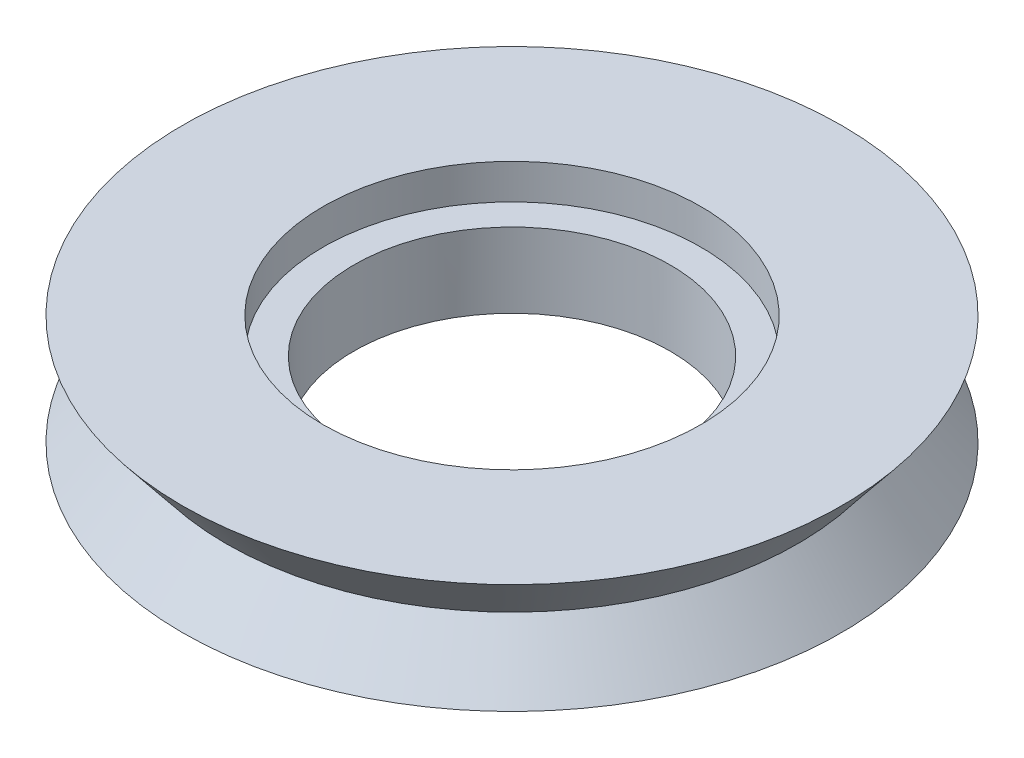
SolidWorks part; units mm, degrees
ref_plane "정면" through (0, 0, 0) normal (0, 0, 1) x (1, 0, 0)
ref_plane "윗면" through (0, 0, 0) normal (0, 1, 0) x (1, 0, 0)
ref_plane "우측면" through (0, 0, 0) normal (1, 0, 0) x (0, 0, -1)
sketch "스케치1" plane through (0, 0, 0) normal (0, 0, 1) x (1, 0, 0)
  line L0 (0, 0) -> (0, 2.5)
  line L1 (0, 2.5) -> (-7.5, 2.5)
  line L2 (-7.5, 2.5) -> (-6.5, 1.25)
  line L3 (-6.5, 1.25) -> (-7.5, 0)
  line L4 (-7.5, 0) -> (0, 0)
  line L5 (0, 2.5) -> (0, 0) construction
  point P9 (0, 1.25)
  dimension "D1" = 7.5
  dimension "D2" = 6.5
  dimension "D3" = 2.5
revolve "회전1" add sketch "스케치1" angle 360 about L5
sketch "스케치2" plane through (0, 2.5, 0) normal (0, 1, 0) x (1, 0, 0)
  circle A0 centre (0, 0) radius 2
  dimension "D1" = 4
extrude "컷-돌출1" cut sketch "스케치2" against normal up to surface (2.5 mm away) up to face at (0, 0, 7.5)
sketch "스케치3" plane through (0, 2.5, 0) normal (0, 1, 0) x (1, 0, 0)
  circle A0 centre (0, 0) radius 3.6
  dimension "D1" = 7.2
extrude "컷-돌출2" cut sketch "스케치3" against normal up to surface (2.5 mm away) up to face at (0, 0, -2)
sketch "스케치4" plane through (0, 2.5, 0) normal (0, 1, 0) x (1, 0, 0)
  circle A0 centre (0, 0) radius 4.3
  dimension "D1" = 8.6
extrude "컷-돌출3" cut sketch "스케치4" against normal blind 0.8
